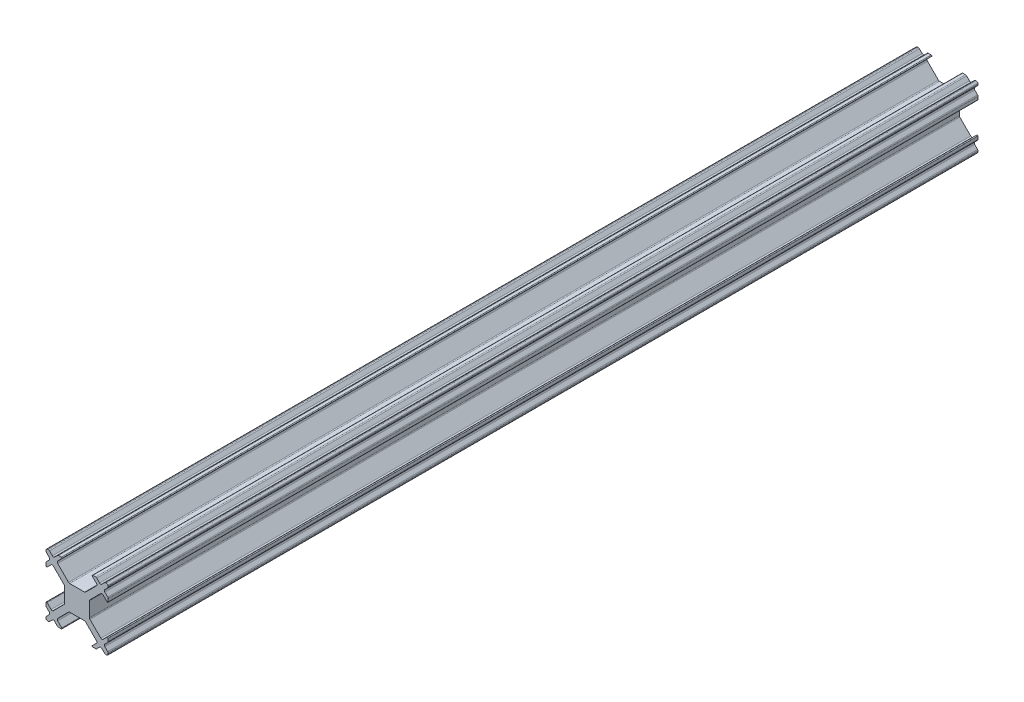
SolidWorks part; units mm, degrees
ref_plane "Front Plane" through (0, 0, 0) normal (0, 0, 1) x (1, 0, 0)
ref_plane "Top Plane" through (0, 0, 0) normal (0, 1, 0) x (1, 0, 0)
ref_plane "Right Plane" through (0, 0, 0) normal (1, 0, 0) x (0, 0, -1)
sketch "Sketch1" plane through (0, 0, 0) normal (0, 0, 1) x (1, 0, 0)
  line L0 (-26.4346, 28.4965) -> (-25.9796, 28.9515)
  line L1 (-25.1311, 29.8) -> (-24.676, 30.2551)
  line L2 (-24.676, 20.4015) -> (-25.1311, 20.8565)
  line L3 (-25.9796, 21.7051) -> (-26.4346, 22.1601)
  line L4 (-26.5078, 30.0783) -> (-26.5078, 29.9369)
  line L5 (-26.5078, 28.3197) -> (-26.5078, 27.8626)
  line L6 (-26.5078, 22.794) -> (-26.5078, 22.3369)
  line L7 (-26.5078, 20.7197) -> (-26.5078, 20.5783)
  line L8 (-23.9714, 30.1576) -> (-24.624, 29.5051)
  line L9 (-25.6846, 28.4444) -> (-26.3371, 27.7919)
  line L10 (-26.2578, 20.3283) -> (-26.1164, 20.3283)
  line L11 (-24.4993, 20.3283) -> (-24.0422, 20.3283)
  line L12 (-18.9735, 20.3283) -> (-18.5164, 20.3283)
  line L13 (-16.8993, 20.3283) -> (-16.7578, 20.3283)
  line L14 (-26.3371, 22.8647) -> (-25.6846, 22.2122)
  line L15 (-24.624, 21.1515) -> (-23.9714, 20.499)
  line L16 (-23.5078, 26.5176) -> (-23.5078, 24.139)
  line L17 (-22.6972, 23.3283) -> (-20.3185, 23.3283)
  line L18 (-25.3311, 22.2122) -> (-23.5811, 23.9622)
  line L19 (-20.1417, 27.4015) -> (-18.3917, 29.1515)
  line L20 (-18.3917, 21.5051) -> (-20.1417, 23.2551)
  line L21 (-23.5811, 26.6944) -> (-25.3311, 28.4444)
  line L22 (-26.4346, 20.8965) -> (-25.9796, 21.3515)
  line L23 (-17.5311, 29.8) -> (-17.076, 30.2551)
  line L24 (-17.076, 20.4015) -> (-17.5311, 20.8565)
  line L25 (-25.9796, 29.3051) -> (-26.4346, 29.7601)
  line L26 (-16.5811, 29.7601) -> (-17.0361, 29.3051)
  line L27 (-25.4846, 20.8565) -> (-25.9396, 20.4015)
  line L28 (-17.6846, 28.4444) -> (-19.4346, 26.6944)
  line L29 (-22.874, 23.2551) -> (-24.624, 21.5051)
  line L30 (-25.9396, 30.2551) -> (-25.4846, 29.8)
  line L31 (-17.0361, 21.3515) -> (-16.5811, 20.8965)
  line L32 (-24.624, 29.1515) -> (-22.874, 27.4015)
  line L33 (-19.4346, 23.9622) -> (-17.6846, 22.2122)
  line L34 (-19.5078, 24.139) -> (-19.5078, 26.5176)
  line L35 (-20.3185, 27.3283) -> (-22.6972, 27.3283)
  line L36 (-16.5078, 20.5783) -> (-16.5078, 20.7197)
  line L37 (-16.5078, 22.3369) -> (-16.5078, 22.794)
  line L38 (-16.5078, 27.8626) -> (-16.5078, 28.3197)
  line L39 (-16.5078, 29.9369) -> (-16.5078, 30.0783)
  line L40 (-16.7578, 30.3283) -> (-16.8993, 30.3283)
  line L41 (-18.5164, 30.3283) -> (-18.9735, 30.3283)
  line L42 (-24.0422, 30.3283) -> (-24.4993, 30.3283)
  line L43 (-26.1164, 30.3283) -> (-26.2578, 30.3283)
  line L44 (-19.0442, 20.499) -> (-18.3917, 21.1515)
  line L45 (-17.3311, 22.2122) -> (-16.6786, 22.8647)
  line L46 (-16.6786, 27.7919) -> (-17.3311, 28.4444)
  line L47 (-18.3917, 29.5051) -> (-19.0442, 30.1576)
  line L48 (-16.5811, 22.1601) -> (-17.0361, 21.7051)
  line L49 (-17.8846, 20.8565) -> (-18.3396, 20.4015)
  line L50 (-18.3396, 30.2551) -> (-17.8846, 29.8)
  line L51 (-17.0361, 28.9515) -> (-16.5811, 28.4965)
  arc A0 (-16.5078, 30.0783) -> (-16.7578, 30.3283) centre (-16.7578, 30.0783) ccw
  arc A1 (-26.2578, 30.3283) -> (-26.5078, 30.0783) centre (-26.2578, 30.0783) ccw
  arc A2 (-16.7578, 20.3283) -> (-16.5078, 20.5783) centre (-16.7578, 20.5783) ccw
  arc A3 (-26.5078, 20.5783) -> (-26.2578, 20.3283) centre (-26.2578, 20.5783) ccw
  arc A4 (-18.9735, 30.3283) -> (-19.0442, 30.1576) centre (-18.9735, 30.2283) ccw
  arc A5 (-16.6786, 27.7919) -> (-16.5078, 27.8626) centre (-16.6078, 27.8626) ccw
  arc A6 (-16.5078, 22.794) -> (-16.6786, 22.8647) centre (-16.6078, 22.794) ccw
  arc A7 (-19.0442, 20.499) -> (-18.9735, 20.3283) centre (-18.9735, 20.4283) ccw
  arc A8 (-26.3371, 22.8647) -> (-26.5078, 22.794) centre (-26.4078, 22.794) ccw
  arc A9 (-26.5078, 27.8626) -> (-26.3371, 27.7919) centre (-26.4078, 27.8626) ccw
  arc A10 (-23.9714, 30.1576) -> (-24.0422, 30.3283) centre (-24.0422, 30.2283) ccw
  arc A11 (-24.0422, 20.3283) -> (-23.9714, 20.499) centre (-24.0422, 20.4283) ccw
  arc A12 (-22.874, 27.4015) -> (-22.6972, 27.3283) centre (-22.6972, 27.5783) ccw
  arc A13 (-20.3185, 27.3283) -> (-20.1417, 27.4015) centre (-20.3185, 27.5783) ccw
  arc A14 (-19.5078, 24.139) -> (-19.4346, 23.9622) centre (-19.2578, 24.139) ccw
  arc A15 (-17.6846, 22.2122) -> (-17.3311, 22.2122) centre (-17.5078, 22.389) ccw
  arc A16 (-22.6972, 23.3283) -> (-22.874, 23.2551) centre (-22.6972, 23.0783) ccw
  arc A17 (-20.1417, 23.2551) -> (-20.3185, 23.3283) centre (-20.3185, 23.0783) ccw
  arc A18 (-25.3311, 28.4444) -> (-25.6846, 28.4444) centre (-25.5078, 28.2676) ccw
  arc A19 (-23.5811, 23.9622) -> (-23.5078, 24.139) centre (-23.7578, 24.139) ccw
  arc A20 (-23.5078, 26.5176) -> (-23.5811, 26.6944) centre (-23.7578, 26.5176) ccw
  arc A21 (-25.6846, 22.2122) -> (-25.3311, 22.2122) centre (-25.5078, 22.389) ccw
  arc A22 (-24.624, 21.5051) -> (-24.624, 21.1515) centre (-24.4472, 21.3283) ccw
  arc A23 (-18.3917, 21.1515) -> (-18.3917, 21.5051) centre (-18.5685, 21.3283) ccw
  arc A24 (-18.3917, 29.1515) -> (-18.3917, 29.5051) centre (-18.5685, 29.3283) ccw
  arc A25 (-17.3311, 28.4444) -> (-17.6846, 28.4444) centre (-17.5078, 28.2676) ccw
  arc A26 (-19.4346, 26.6944) -> (-19.5078, 26.5176) centre (-19.2578, 26.5176) ccw
  arc A27 (-24.624, 29.5051) -> (-24.624, 29.1515) centre (-24.4472, 29.3283) ccw
  arc A28 (-17.0361, 29.3051) -> (-17.0361, 28.9515) centre (-16.8593, 29.1283) ccw
  arc A29 (-17.0361, 21.7051) -> (-17.0361, 21.3515) centre (-16.8593, 21.5283) ccw
  arc A30 (-25.4846, 29.8) -> (-25.1311, 29.8) centre (-25.3078, 29.9768) ccw
  arc A31 (-17.8846, 29.8) -> (-17.5311, 29.8) centre (-17.7078, 29.9768) ccw
  arc A32 (-25.9796, 28.9515) -> (-25.9796, 29.3051) centre (-26.1564, 29.1283) ccw
  arc A33 (-25.9796, 21.3515) -> (-25.9796, 21.7051) centre (-26.1564, 21.5283) ccw
  arc A34 (-17.5311, 20.8565) -> (-17.8846, 20.8565) centre (-17.7078, 20.6798) ccw
  arc A35 (-25.1311, 20.8565) -> (-25.4846, 20.8565) centre (-25.3078, 20.6798) ccw
  arc A36 (-18.3396, 30.2551) -> (-18.5164, 30.3283) centre (-18.5164, 30.0783) ccw
  arc A37 (-16.8993, 30.3283) -> (-17.076, 30.2551) centre (-16.8993, 30.0783) ccw
  arc A38 (-24.4993, 30.3283) -> (-24.676, 30.2551) centre (-24.4993, 30.0783) ccw
  arc A39 (-25.9396, 30.2551) -> (-26.1164, 30.3283) centre (-26.1164, 30.0783) ccw
  arc A40 (-26.5078, 29.9369) -> (-26.4346, 29.7601) centre (-26.2578, 29.9369) ccw
  arc A41 (-26.4346, 28.4965) -> (-26.5078, 28.3197) centre (-26.2578, 28.3197) ccw
  arc A42 (-26.4346, 20.8965) -> (-26.5078, 20.7197) centre (-26.2578, 20.7197) ccw
  arc A43 (-26.5078, 22.3369) -> (-26.4346, 22.1601) centre (-26.2578, 22.3369) ccw
  arc A44 (-24.676, 20.4015) -> (-24.4993, 20.3283) centre (-24.4993, 20.5783) ccw
  arc A45 (-18.5164, 20.3283) -> (-18.3396, 20.4015) centre (-18.5164, 20.5783) ccw
  arc A46 (-17.076, 20.4015) -> (-16.8993, 20.3283) centre (-16.8993, 20.5783) ccw
  arc A47 (-16.5078, 28.3197) -> (-16.5811, 28.4965) centre (-16.7578, 28.3197) ccw
  arc A48 (-16.5078, 20.7197) -> (-16.5811, 20.8965) centre (-16.7578, 20.7197) ccw
  arc A49 (-16.5811, 22.1601) -> (-16.5078, 22.3369) centre (-16.7578, 22.3369) ccw
  arc A50 (-16.5811, 29.7601) -> (-16.5078, 29.9369) centre (-16.7578, 29.9369) ccw
  arc A51 (-26.1164, 20.3283) -> (-25.9396, 20.4015) centre (-26.1164, 20.5783) ccw
  dimension "D1" = 4
  dimension "D2" = 10
extrude "Boss-Extrude1" add sketch "Sketch1" along normal blind 140
